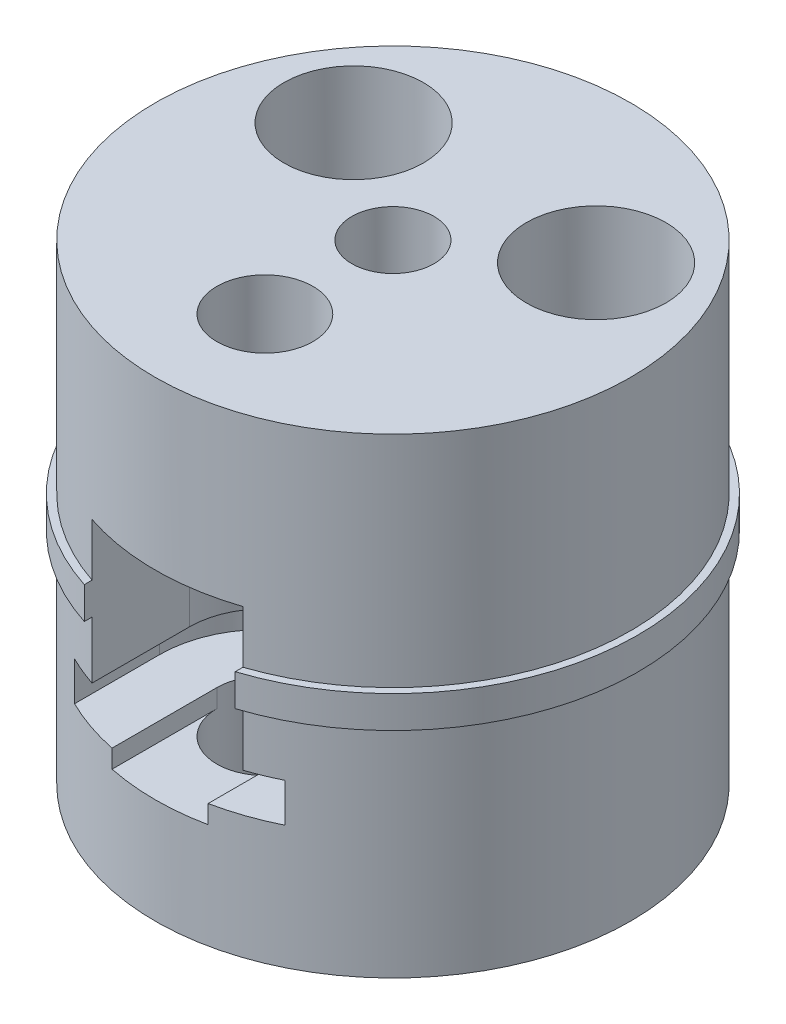
SolidWorks part; units mm, degrees
ref_plane "Front Plane" through (0, 0, 0) normal (0, 0, 1) x (1, 0, 0)
ref_plane "Top Plane" through (0, 0, 0) normal (0, 1, 0) x (1, 0, 0)
ref_plane "Right Plane" through (0, 0, 0) normal (1, 0, 0) x (0, 0, -1)
sketch "Sketch1" plane through (0, 0, 0) normal (0, 1, 0) x (1, 0, 0)
  circle A0 centre (0, 0) radius 26.797
  dimension "D1" = 53.594
extrude "Boss-Extrude1" add sketch "Sketch1" along normal blind 3.5
sketch "Sketch2" plane through (0, 3.5, 0) normal (0, 1, 0) x (1, 0, 0)
  circle A0 centre (0, 0) radius 25.9969
  dimension "D1" = 51.9938
extrude "Boss-Extrude2" add sketch "Sketch2" along normal blind 24
sketch "Sketch3" plane through (0, 0, 0) normal (0, -1, 0) x (1, 0, 0)
  circle A1 centre (0, 0) radius 25.9969 construction
  circle A2 centre (0, 0) radius 25.9969
extrude "Boss-Extrude3" add sketch "Sketch3" along normal blind 24
sketch "Sketch4" plane through (0, -24, 0) normal (0, -1, 0) x (1, 0, 0)
  line L0 (-13.2559, -8.9599) -> (0, 14) construction
  line L1 (0, 14) -> (13.2559, -8.9599) construction
  line L2 (13.2559, -8.9599) -> (-13.2559, -8.9599) construction
  circle A0 centre (-13.2559, -8.9599) radius 7.625
  circle A1 centre (0, 14) radius 4 construction
  circle A2 centre (-13.2559, -8.9599) radius 4 construction
  circle A3 centre (13.2559, -8.9599) radius 4 construction
  circle A4 centre (13.2559, -8.9599) radius 7.625
  circle A5 centre (0, 14) radius 7 construction
  circle A6 centre (0, 0) radius 7 construction
  dimension "D3" = 8
  dimension "D4" = 15.25
  dimension "D1" = 14
  dimension "D2" = 16
sketch "Sketch5" plane through (0, 27.5, -30.35) normal (0, -1, 0) x (-1, 0, 0)
  line L0 (-13.2559, -21.3901) -> (0, -44.35) construction
  line L1 (0, -44.35) -> (13.2559, -21.3901) construction
  line L2 (13.2559, -21.3901) -> (-13.2559, -21.3901) construction
  line L4 (3.175, -33.525) -> (-3.175, -33.525) construction
  line L5 (3.175, -33.525) -> (3.175, -27.175) construction
  line L6 (3.175, -27.175) -> (-3.175, -27.175) construction
  line L7 (-3.175, -33.525) -> (-3.175, -27.175) construction
  line L8 (3.175, -33.525) -> (-3.175, -27.175) construction
  line L9 (3.175, -27.175) -> (-3.175, -33.525) construction
  circle A0 centre (-13.2559, -21.3901) radius 7.625
  circle A1 centre (0, -44.35) radius 4 construction
  circle A2 centre (-13.2559, -21.3901) radius 4 construction
  circle A3 centre (13.2559, -21.3901) radius 4 construction
  circle A4 centre (13.2559, -21.3901) radius 7.625
  circle A5 centre (0, -44.35) radius 7 construction
  circle A6 centre (0, -30.35) radius 7 construction
  circle A7 centre (0, -30.35) radius 4.4901
  dimension "D3" = 8
  dimension "D4" = 15.25
  dimension "D1" = 14
  dimension "D2" = 16
  dimension "D5" = 6.35
sketch "Sketch6" plane through (0, -24, -24) normal (0, 1, 0) x (-1, 0, 0)
  line L0 (-13.2559, 15.0401) -> (0, 38) construction
  line L1 (0, 38) -> (13.2559, 15.0401) construction
  line L2 (13.2559, 15.0401) -> (-13.2559, 15.0401) construction
  circle A0 centre (-13.2559, 15.0401) radius 7.5 construction
  circle A1 centre (0, 38) radius 5.25
  circle A2 centre (-13.2559, 15.0401) radius 5
  circle A3 centre (13.2559, 15.0401) radius 5
  circle A4 centre (13.2559, 15.0401) radius 7.5 construction
  circle A5 centre (0, 38) radius 7 construction
  circle A6 centre (0, 24) radius 7 construction
  dimension "D3" = 10
  dimension "D4" = 15
  dimension "D5" = 10.5
  dimension "D1" = 14
  dimension "D2" = 16
extrude "Cut-Extrude1" cut sketch "Sketch4" against normal up to surface (24 mm away) up to face at (0, 0, -25.9969)
extrude "Cut-Extrude2" cut sketch "Sketch5" along normal up to surface (24 mm away) up to face at (0, 3.5, 25.9969)
extrude "Cut-Extrude4" cut sketch "Sketch6" along normal through all
ref_plane "Plane1" through (0, 0, 26.797) normal (0, 0, 1) x (1, 0, 0)
sketch "Sketch7" plane through (0, 0, 26.797) normal (0, 0, 1) x (1, 0, 0)
  line L0 (26.797, 3.5) -> (-26.797, 3.5) construction
  line L1 (-8.25, 3.5) -> (8.25, 3.5)
  line L2 (-8.25, 3.5) -> (-8.25, 9.25)
  line L3 (-8.25, 9.25) -> (8.25, 9.25)
  line L4 (8.25, 3.5) -> (8.25, 9.25)
  line L5 (-8.25, 3.5) -> (8.25, 9.25) construction
  line L6 (-8.25, 9.25) -> (8.25, 3.5) construction
  point P0 (0, 6.375)
  dimension "D1" = 5.75
  dimension "D2" = 16.5
extrude "Cut-Extrude5" cut sketch "Sketch7" against normal up to surface (26.797 mm away)
sketch "Sketch8" plane through (0, 3.5, 0) normal (0, 1, 0) x (1, 0, 0)
  line L1 (-8.25, 0) -> (8.25, 0)
  arc A0 (-8.25, 0) -> (8.25, 0) centre (0, 0) cw
extrude "Cut-Extrude6" cut sketch "Sketch8" along normal up to surface (5.75 mm away) up to face at (0, 9.25, 19.25)
sketch "Sketch9" plane through (0, 0, 26.797) normal (0, 0, 1) x (1, 0, 0)
  line L6 (-11.5, -10.5) -> (11.5, -10.5)
  line L7 (-11.5, -10.5) -> (-11.5, -6.25)
  line L8 (-11.5, -6.25) -> (11.5, -6.25)
  line L9 (11.5, -10.5) -> (11.5, -6.25)
  line L10 (-11.5, -10.5) -> (11.5, -6.25) construction
  line L11 (-11.5, -6.25) -> (11.5, -10.5) construction
  point P0 (0, -8.375)
  dimension "D1" = 4.25
  dimension "D2" = 23
  dimension "D3" = 15.5
ref_point "Point1"
sketch "Sketch13" plane through (0, 0, 26.797) normal (0, 0, 1) x (1, 0, 0)
  line L1 (-8.25, 3.5) -> (8.25, 3.5)
  line L2 (-8.25, 3.5) -> (-8.25, -6.25)
  line L3 (-8.25, -6.25) -> (8.25, -6.25)
  line L4 (8.25, 3.5) -> (8.25, -6.25)
  dimension "D1" = 15.5
extrude "Cut-Extrude10" cut sketch "Sketch13" against normal up to vertex (12.797 mm away)
sketch "Sketch14" plane through (0, -6.25, 0) normal (0, 1, 0) x (1, 0, 0)
  line L0 (-8.25, -14) -> (8.25, -14)
  arc A0 (-8.25, -14) -> (8.25, -14) centre (0, -14) cw
extrude "Cut-Extrude11" cut sketch "Sketch14" along normal up to surface (9.75 mm away) up to face at (0, 3.5, -0.6613)
extrude "Cut-Extrude7" cut sketch "Sketch9" against normal up to vertex (12.797 mm away)
sketch "Sketch11" plane through (0, -10.5, 0) normal (0, 1, 0) x (1, 0, 0)
  line L0 (5.25, -14) -> (11.5, -14) construction
  line L1 (-11.5, -14) -> (11.5, -14)
  arc A0 (-11.5, -14) -> (11.5, -14) centre (0, -14) cw
extrude "Cut-Extrude8" cut sketch "Sketch11" along normal up to surface (4.25 mm away) up to face at (9.8807, -6.25, 19.0058)
sketch "Sketch12" plane through (0, 0, 26.797) normal (0, 0, 1) x (1, 0, 0)
  line L0 (11.5, -10.5) -> (-11.5, -10.5) construction
  line L1 (5.25, -12.5) -> (-5.25, -12.5)
  line L2 (5.25, -12.5) -> (5.25, -10.5)
  line L3 (5.25, -10.5) -> (-5.25, -10.5)
  line L4 (-5.25, -12.5) -> (-5.25, -10.5)
  line L5 (5.25, -12.5) -> (-5.25, -10.5) construction
  line L6 (5.25, -10.5) -> (-5.25, -12.5) construction
  point P0 (0, -11.5)
  dimension "D1" = 10.5
  dimension "D3" = 2
extrude "Cut-Extrude9" cut sketch "Sketch12" against normal up to vertex
